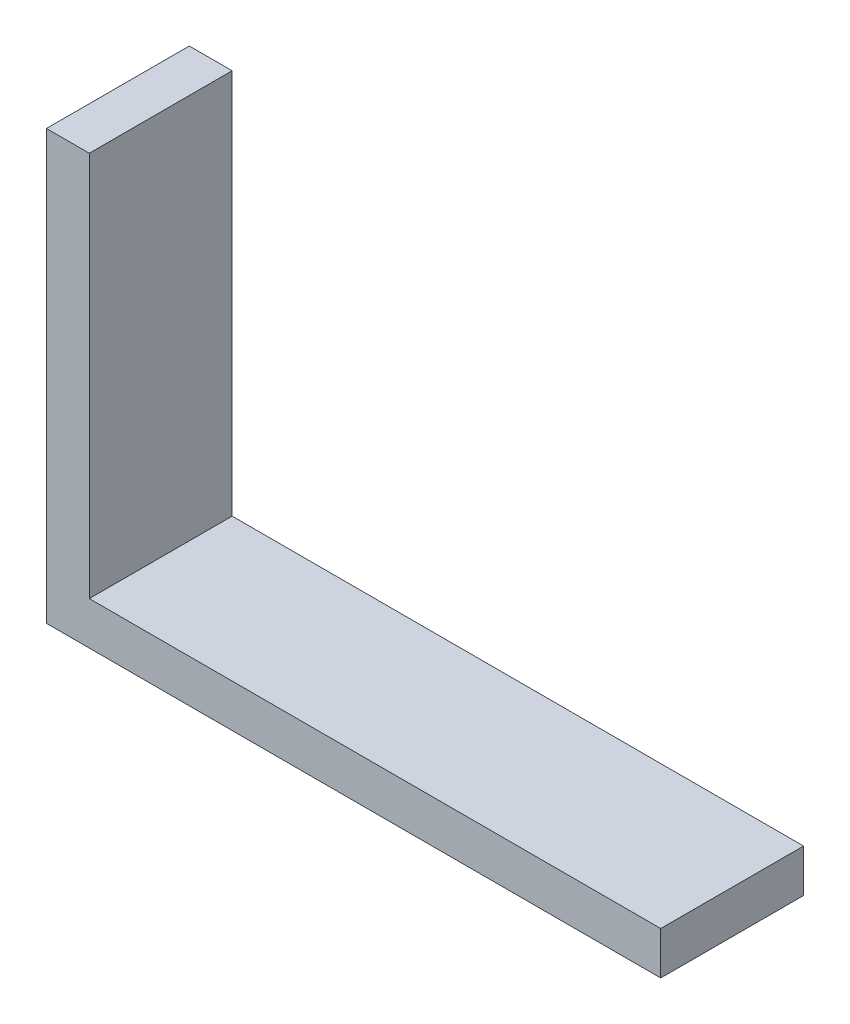
SolidWorks part; units mm, degrees
ref_plane "Front Plane" through (0, 0, 0) normal (0, 0, 1) x (1, 0, 0)
ref_plane "Top Plane" through (0, 0, 0) normal (0, 1, 0) x (1, 0, 0)
ref_plane "Right Plane" through (0, 0, 0) normal (1, 0, 0) x (0, 0, -1)
sketch "Sketch1" plane through (0, 0, 0) normal (0, 0, 1) x (1, 0, 0)
  line L0 (0, 0) -> (0, 30)
  line L1 (0, 30) -> (3, 30)
  line L2 (3, 30) -> (3, 3)
  line L3 (3, 3) -> (43, 3)
  line L4 (43, 3) -> (43, 0)
  line L5 (43, 0) -> (0, 0)
  dimension "D1" = 30
  dimension "D2" = 3
  dimension "D3" = 3
  dimension "D4" = 40
extrude "Boss-Extrude1" add sketch "Sketch1" along normal blind 10
